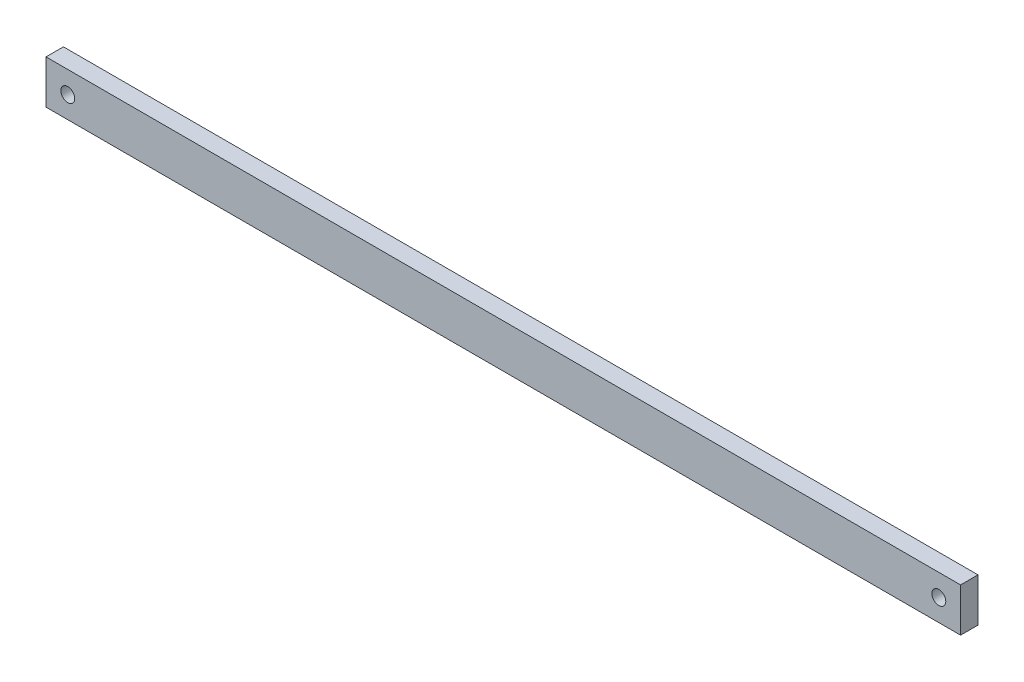
SolidWorks part; units mm, degrees
ref_plane "前视基准面" through (0, 0, 0) normal (0, 0, 1) x (1, 0, 0)
ref_plane "上视基准面" through (0, 0, 0) normal (0, 1, 0) x (1, 0, 0)
ref_plane "右视基准面" through (0, 0, 0) normal (1, 0, 0) x (0, 0, -1)
sketch "草图1" plane through (0, 0, 0) normal (0, 0, 1) x (1, 0, 0)
  line L0 (-105, 0) -> (105, 0) construction
  line L1 (105, -5) -> (-105, -5)
  line L2 (105, -5) -> (105, 5)
  line L3 (105, 5) -> (-105, 5)
  line L4 (-105, -5) -> (-105, 5)
  line L5 (105, -5) -> (-105, 5) construction
  line L6 (105, 5) -> (-105, -5) construction
  line L7 (0, 5) -> (0, -5) construction
  circle A0 centre (-100, 0) radius 1.6
  circle A1 centre (100, 0) radius 1.6
  point P0 (0, 0)
  dimension "D3" = 100
  dimension "D1" = 10
  dimension "D2" = 210
extrude "凸台-拉伸1" add sketch "草图1" along normal blind 4
